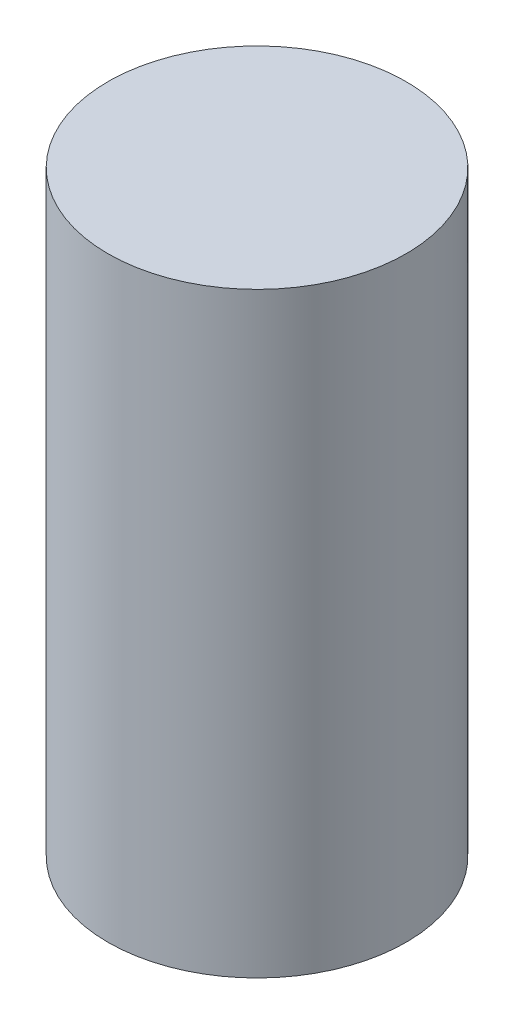
SolidWorks part; units mm, degrees
ref_plane "Front Plane" through (0, 0, 0) normal (0, 0, 1) x (1, 0, 0)
ref_plane "Top Plane" through (0, 0, 0) normal (0, 1, 0) x (1, 0, 0)
ref_plane "Right Plane" through (0, 0, 0) normal (1, 0, 0) x (0, 0, -1)
sketch "Sketch1" plane through (0, 0, 0) normal (0, 1, 0) x (1, 0, 0)
  circle A0 centre (0, 0) radius 0.25
  point P2 (0, 0)
  dimension "D1" = 0.5
extrude "Boss-Extrude1" add sketch "Sketch1" along normal blind 1
sketch "Sketch2" plane through (0, 0, 0) normal (1, 0, 0) x (0, 0, -1)
  line L0 (-0.25, 0.5) -> (0.25, 0.5) construction
  line L2 (0.25, 0) -> (0.25, 1) construction
  line L3 (-0.25, 1) -> (-0.25, 0) construction
  point P4 (-0.25, 0.5)
sketch "Sketch3" plane through (0, 0, 0) normal (0, -1, 0) x (-1, 0, 0)
  line L0 (0, 0.25) -> (0, -0.25) construction
  circle A0 centre (0, 0) radius 0.25 construction
